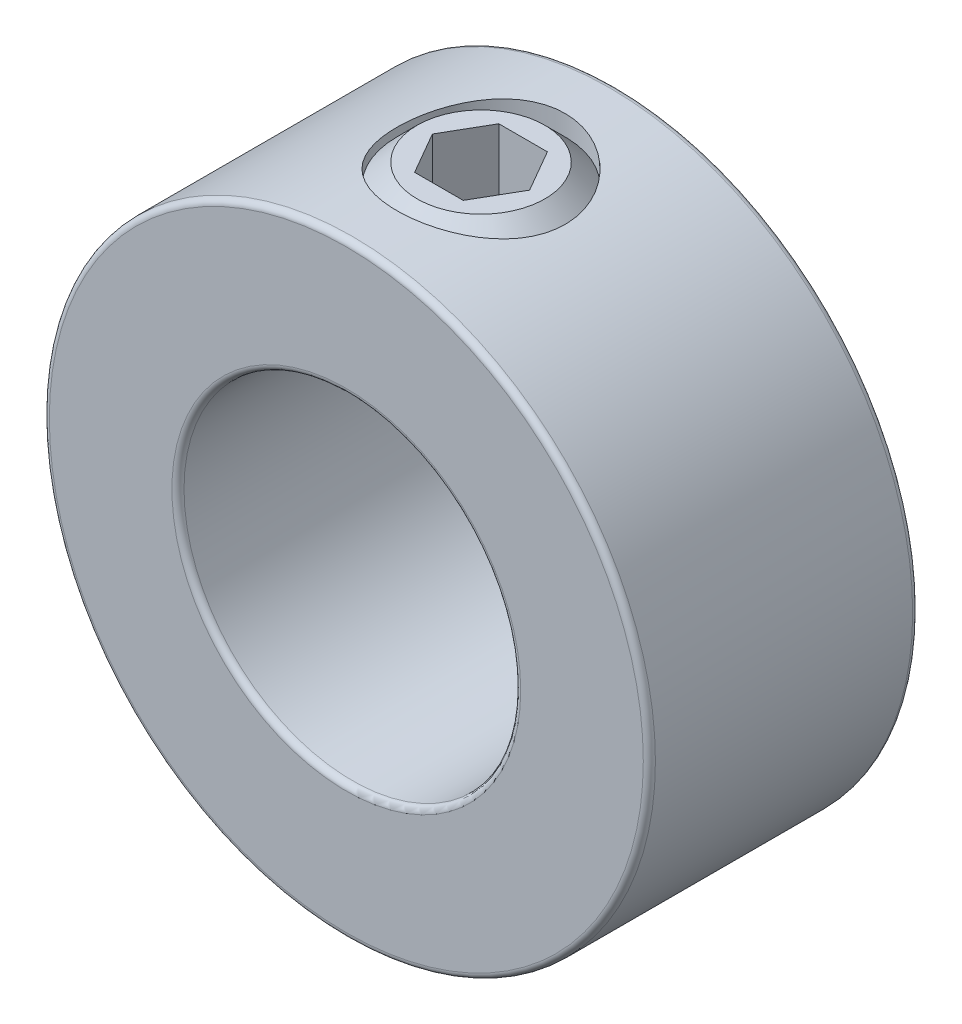
SolidWorks part; units mm, degrees
ref_plane "Front Plane" through (0, 0, 0) normal (0, 0, 1) x (1, 0, 0)
ref_plane "Top Plane" through (0, 0, 0) normal (0, 1, 0) x (1, 0, 0)
ref_plane "Right Plane" through (0, 0, 0) normal (1, 0, 0) x (0, 0, -1)
sketch "Sketch1" plane through (0, 0, 0) normal (0, 0, 1) x (1, 0, 0)
  circle A0 centre (0, 0) radius 14.2875
  circle A1 centre (0, 0) radius 7.9375
  point P4 (14.2875, 0)
  dimension "Bore Dia" = 15.875
  dimension "OD" = 28.575
extrude "Extrude1" add sketch "Sketch1" along normal mid plane 12.7
sketch "Sketch2" plane through (41.275, 0, 0) normal (0, -1, 0) x (0, 0, -1)
  line L0 (6.35, -41.275) -> (-6.35, -41.275) construction
  line L1 (-6.35, -26.9875) -> (-6.35, -55.5625) construction
  line L2 (6.35, -55.5625) -> (6.35, -26.9875) construction
  circle A0 centre (0, -41.275) radius 3.9688
  point P7 (0, -45.2437)
  dimension "Set Screw Dia" = 7.9375
extrude "Cut-Extrude1" cut sketch "Sketch2" against normal through all
fillet "Fillet1" radius 0.2858 4 edges at (7.9375, 0, -6.35) (7.9375, 0, 6.35) (14.2875, 0, -6.35) (14.2875, 0, 6.35)
sketch "Sketch3" plane through (0, 0, 0) normal (0, 0, 1) x (1, 0, 0)
  line L0 (-3.0102, 7.9375) -> (-1.1502, 7.9375)
  line L1 (0, 9.0877) -> (-1.1502, 7.9375)
  line L2 (0, 9.0877) -> (0, 14.2875)
  line L3 (0, 14.2875) -> (-3.0102, 14.2875)
  line L4 (-3.9688, 8.896) -> (-3.9688, 13.329)
  line L5 (0, 7.9375) -> (0, 0) construction
  line L6 (-3.9688, 8.896) -> (-3.9688, 7.9375) construction
  line L7 (-3.9688, 7.9375) -> (-3.0102, 7.9375) construction
  line L8 (-3.9688, 13.329) -> (-3.9688, 14.2875) construction
  line L9 (-3.0102, 7.9375) -> (-3.9688, 8.896)
  line L10 (-3.9688, 13.329) -> (-3.0102, 14.2875)
  line L11 (-3.9688, 14.2875) -> (-3.0102, 14.2875) construction
  line L12 (-1.1502, 7.9375) -> (0, 7.9375) construction
  line L13 (0, 7.9375) -> (0, 9.0877) construction
  circle A1 centre (0, 0) radius 7.9375 construction
  dimension "Screw Length" = 6.35
  dimension "D2" = 0.9585
  dimension "D1" = 1.1502
revolve "Revolve1" add sketch "Sketch3" angle 360 about L5
sketch "Sketch4" plane through (3.3734, 14.2875, 0) normal (0, -1, 0) x (0, 0, -1)
  line L1 (0, -1.0821) -> (-1.9844, -2.2278)
  line L2 (-1.9844, -2.2278) -> (-1.9844, -4.5191)
  line L3 (-1.9844, -4.5191) -> (0, -5.6648)
  line L4 (0, -5.6648) -> (1.9844, -4.5191)
  line L5 (1.9844, -4.5191) -> (1.9844, -2.2278)
  line L6 (1.9844, -2.2278) -> (0, -1.0821)
  circle A0 centre (0, -3.3734) radius 1.9844 construction
  circle A1 centre (0, -3.3734) radius 2.2914 construction
  dimension "D1" = 4.5827
  dimension "Hex Size" = 3.9688
extrude "Cut-Extrude2" cut sketch "Sketch4" along normal blind 3.9688
equation "\"D1@Fillet1\" = \"OD@Sketch1\"*.01"
equation "\"D1@Cut-Extrude2\" = \"Hex Size@Sketch4\""
equation "\"D2@Sketch3\" =(\"Set Screw Dia@Sketch2\"-\"D1@Sketch4\")/3.5"
equation "\"D1@Sketch3\" = \"D2@Sketch3\"*1.2"
